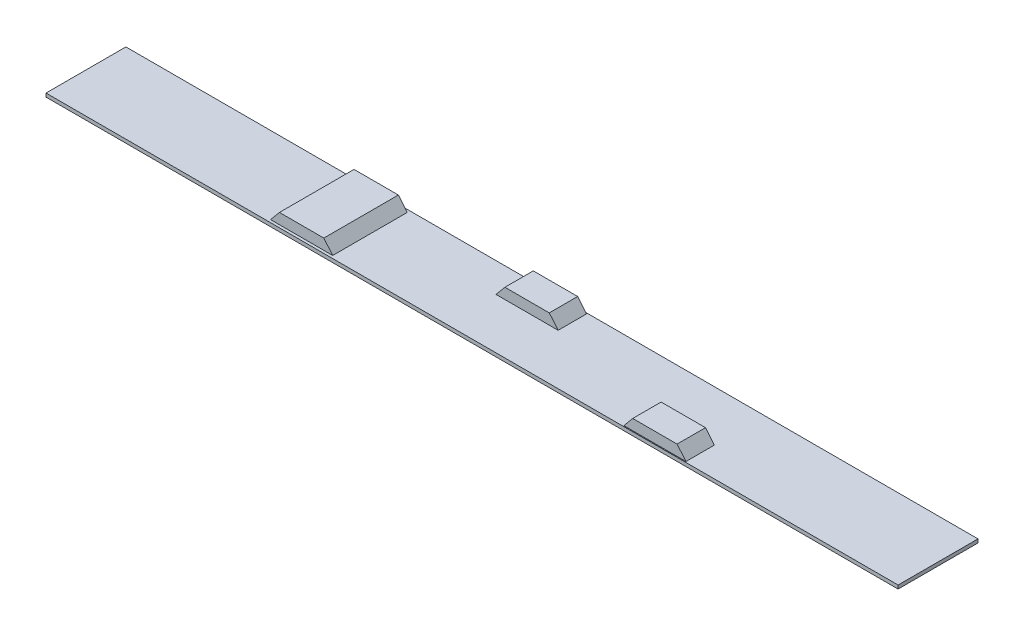
SolidWorks part; units mm, degrees
ref_plane "Front Plane" through (0, 0, 0) normal (0, 0, 1) x (1, 0, 0)
ref_plane "Top Plane" through (0, 0, 0) normal (0, 1, 0) x (1, 0, 0)
ref_plane "Right Plane" through (0, 0, 0) normal (1, 0, 0) x (0, 0, -1)
sketch "Sketch1" plane through (0, 0, 0) normal (0, 1, 0) x (1, 0, 0)
  line L1 (-1200, 112.5) -> (1200, 112.5)
  line L2 (-1200, 112.5) -> (-1200, -112.5)
  line L3 (-1200, -112.5) -> (1200, -112.5)
  line L4 (1200, 112.5) -> (1200, -112.5)
  line L5 (-1200, 112.5) -> (1200, -112.5) construction
  line L6 (-1200, -112.5) -> (1200, 112.5) construction
  point P0 (0, 0)
  dimension "D1" = 2400
  dimension "D2" = 225
extrude "Boss-Extrude1" add sketch "Sketch1" along normal blind 10
sketch "Sketch8" plane through (0, 0, 0) normal (0, 0, 1) x (1, 0, 0)
  line L0 (425, 10) -> (450, 40)
  line L1 (-1200, 10) -> (1200, 10) construction
  line L2 (450, 40) -> (575, 40)
  line L3 (575, 40) -> (600, 10)
  line L4 (600, 10) -> (425, 10)
  point P4 (512.5, 40)
  point P7 (512.5, 10)
  dimension "D1" = 175
  dimension "D2" = 125
  dimension "D3" = 30
  dimension "D4" = 600
extrude "Boss-Extrude4" add sketch "Sketch8" along normal blind 80 from offset 30
sketch "Sketch14" plane through (0, 0, 0) normal (0, 0, 1) x (1, 0, 0)
  line L0 (0, 0) -> (-500, 0) construction
  line L1 (-75, 10) -> (100, 10)
  line L2 (100, 10) -> (75, 40)
  line L3 (75, 40) -> (-50, 40)
  line L4 (425, 10) -> (600, 10)
  line L5 (600, 10) -> (575, 40)
  line L6 (575, 40) -> (450, 40)
  line L7 (450, 40) -> (425, 10)
  line L8 (425, 10) -> (600, 10)
  line L9 (600, 10) -> (575, 40)
  line L10 (575, 40) -> (450, 40)
  line L11 (450, 40) -> (425, 10)
  line L12 (-50, 40) -> (-75, 10)
  line L13 (425, 10) -> (-75, 10) construction
  dimension "D2" = 500
  dimension "D4" = 500
  dimension "D1" = 0
  dimension "D3" = 2
extrude "Boss-Extrude5" add sketch "Sketch14" against normal blind 80 from offset 30 contours L3 L12 L1 L2 offset against normal yes
sketch "Sketch15" plane through (0, 0, 0) normal (0, 0, 1) x (1, 0, 0)
  line L0 (-400, 10) -> (-425, 40)
  line L1 (-425, 40) -> (-550, 40)
  line L2 (-550, 40) -> (-575, 10)
  line L3 (-575, 10) -> (-400, 10)
  line L4 (100, 10) -> (75, 40)
  line L5 (75, 40) -> (-50, 40)
  line L6 (-50, 40) -> (-75, 10)
  line L7 (-75, 10) -> (100, 10)
  line L8 (100, 10) -> (75, 40)
  line L9 (75, 40) -> (-50, 40)
  line L10 (-50, 40) -> (-75, 10)
  line L11 (-75, 10) -> (100, 10)
  line L12 (100, 10) -> (-400, 10) construction
  dimension "D3" = 500
  dimension "D1" = 0
  dimension "D2" = 2
extrude "Boss-Extrude6" add sketch "Sketch15" along normal blind 105 and the other way blind 105 contours L0 L1 L2 L3
